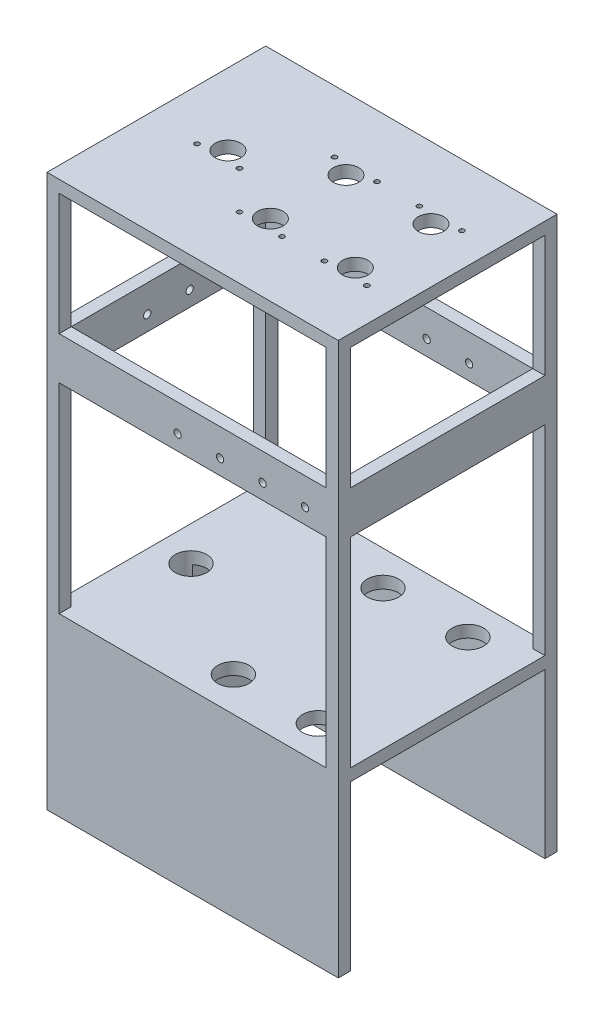
SolidWorks part; units mm, degrees
ref_plane "Front Plane" through (0, 0, 0) normal (0, 0, 1) x (1, 0, 0)
ref_plane "Top Plane" through (0, 0, 0) normal (0, 1, 0) x (1, 0, 0)
ref_plane "Right Plane" through (0, 0, 0) normal (1, 0, 0) x (0, 0, -1)
sketch "Sketch1" plane through (0, 0, 0) normal (0, 1, 0) x (1, 0, 0)
  line L0 (0, 90.15) -> (0, -90.15) construction
  line L1 (-120.075, 0) -> (120.075, 0) construction
  line L2 (-120.075, 90.15) -> (120.075, 90.15)
  line L3 (120.075, 90.15) -> (120.075, -90.15)
  line L4 (120.075, -90.15) -> (-120.075, -90.15)
  line L5 (-120.075, -90.15) -> (-120.075, 90.15)
  dimension "D1" = 240.15
  dimension "D2" = 180.3
extrude "Boss-Extrude1" add sketch "Sketch1" along normal blind 145
sketch "Sketch2" plane through (0, 145, 0) normal (0, 1, 0) x (1, 0, 0)
  line L0 (0, 90.15) -> (0, -90.15) construction
  line L1 (120.075, 90.15) -> (-120.075, 90.15) construction
  line L2 (-120.075, -90.15) -> (120.075, -90.15) construction
  line L3 (-120.075, 0) -> (120.075, 0) construction
  line L4 (-120.075, 90.15) -> (-120.075, -90.15) construction
  line L5 (120.075, -90.15) -> (120.075, 90.15) construction
  line L6 (75.105, -61.65) -> (75.105, -90.15) construction
  line L7 (75.105, -61.65) -> (120.075, -61.65) construction
  line L8 (75.105, -61.65) -> (5.105, -61.65) construction
  circle A0 centre (75.105, -61.65) radius 12.955
  circle A1 centre (5.105, -61.65) radius 12.955
  circle A2 centre (75.105, 61.65) radius 12.955
  circle A3 centre (5.105, 61.65) radius 12.955
  circle A4 centre (-91.515, 0) radius 12.955
  dimension "D3" = 25.91
  dimension "D5" = 25.91
  dimension "D6" = 25.91
  dimension "D7" = 28.56
  dimension "D1" = 44.97
  dimension "D2" = 28.5
  dimension "D4" = 70
extrude "Cut-Extrude1" cut sketch "Sketch2" against normal blind 120
sketch "Sketch3" plane through (120.075, 0, 0) normal (1, 0, 0) x (0, 0, -1)
  line L0 (0, 145) -> (0, 0) construction
  line L1 (-90.15, 145) -> (90.15, 145) construction
  line L2 (-90.15, 72.5) -> (90.15, 72.5) construction
  line L3 (-90.15, 145) -> (-90.15, 0) construction
  line L4 (90.15, 145) -> (90.15, 0) construction
  line L5 (-80.21, 135.06) -> (80.21, 135.06)
  line L6 (80.21, 135.06) -> (80.21, 0)
  line L7 (-90.15, 0) -> (90.15, 0) construction
  line L8 (80.21, 0) -> (-80.21, 0)
  line L9 (-80.21, 0) -> (-80.21, 135.06)
  dimension "D1" = 9.94
  dimension "D2" = 9.94
  dimension "D3" = 9.94
extrude "Cut-Extrude3" cut sketch "Sketch3" against normal blind 220
sketch "Sketch9" plane through (0, 145, 0) normal (0, 1, 0) x (1, 0, 0)
  line L0 (-120.075, 90.15) -> (120.075, 90.15)
  line L1 (120.075, 90.15) -> (120.075, -90.15)
  line L2 (120.075, -90.15) -> (-120.075, -90.15)
  line L3 (-120.075, -90.15) -> (-120.075, 90.15)
extrude "Boss-Extrude3" add sketch "Sketch9" along normal blind 310.134
sketch "Sketch14" plane through (0, 455.134, 0) normal (0, 1, 0) x (1, 0, 0)
  line L0 (75.105, 61.65) -> (75.105, 31.17) construction
  line L1 (-91.515, 0) -> (-61.035, 0) construction
  line L2 (75.105, -61.65) -> (75.105, -31.17) construction
  line L3 (5.105, -61.65) -> (5.105, -31.17) construction
  line L4 (5.105, 61.65) -> (5.105, 31.17) construction
  line L5 (-61.035, 0) -> (193.3968, 0) construction
  line L6 (75.105, 31.17) -> (75.105, -31.17) construction
  line L7 (5.105, 31.17) -> (5.105, -31.17) construction
  line L8 (-61.035, 0) -> (-61.035, -46.2698) construction
  circle A0 centre (5.105, -31.17) radius 10.5
  circle A1 centre (75.105, 31.17) radius 10.5
  circle A3 centre (-61.035, 0) radius 10.5
  circle A5 centre (75.105, -31.17) radius 10.5
  circle A6 centre (92.605, -39.14) radius 2
  circle A7 centre (75.105, -61.65) radius 12.955 construction
  circle A8 centre (57.605, -39.14) radius 2
  circle A9 centre (-91.515, 0) radius 12.955 construction
  circle A10 centre (5.105, -61.65) radius 12.955 construction
  circle A11 centre (5.105, 31.17) radius 10.5
  circle A12 centre (5.105, 61.65) radius 12.955 construction
  circle A13 centre (92.605, 39.14) radius 2
  circle A14 centre (57.605, 39.14) radius 2
  circle A15 centre (22.605, -39.14) radius 2
  circle A16 centre (-12.395, -39.14) radius 2
  circle A17 centre (22.605, 39.14) radius 2
  circle A18 centre (-12.395, 39.14) radius 2
  circle A19 centre (-43.535, -7.97) radius 2
  circle A20 centre (-78.535, -7.97) radius 2
  dimension "D2" = 21
  dimension "D3" = 21
  dimension "D5" = 21
  dimension "D6" = 21
  dimension "D7" = 21
  dimension "D8" = 30.48
  dimension "D9" = 30.48
  dimension "D10" = 30.48
  dimension "D4" = 30.48
  dimension "D12" = 17.5
  dimension "D13" = 4
  dimension "D14" = 17.5
  dimension "D15" = 17.5
  dimension "D16" = 7.97
  dimension "D1" = 30.48
  dimension "D11" = 7.97
extrude "Cut-Extrude6" cut sketch "Sketch14" against normal blind 11
sketch "Sketch15" plane through (0, 0, -90.15) normal (0, 0, -1) x (-1, 0, 0)
  line L0 (-120.075, 455.134) -> (120.075, 455.134) construction
  line L1 (-110.075, 445.134) -> (110.075, 445.134)
  line L2 (-110.075, 445.134) -> (-110.075, 344.894)
  line L3 (-110.075, 344.894) -> (110.075, 344.894)
  line L4 (110.075, 445.134) -> (110.075, 344.894)
  line L5 (-120.075, 455.134) -> (-120.075, 0) construction
  line L6 (120.075, 455.134) -> (120.075, 0) construction
  line L7 (-120.075, 0) -> (120.075, 0) construction
  line L8 (-110.075, 309.844) -> (110.075, 309.844)
  line L9 (-110.075, 309.844) -> (-110.075, 145)
  line L10 (-110.075, 145) -> (110.075, 145)
  line L11 (110.075, 309.844) -> (110.075, 145)
  dimension "D1" = 110.24
  dimension "D2" = 10
  dimension "D3" = 10
  dimension "D4" = 10
  dimension "D5" = 35.05
  dimension "D6" = 10
  dimension "D7" = 10
  dimension "D8" = 145
extrude "Cut-Extrude7" cut sketch "Sketch15" against normal through all
sketch "Sketch16" plane through (120.075, 0, 0) normal (1, 0, 0) x (0, 0, -1)
  line L0 (-90.15, 455.134) -> (-90.15, 0) construction
  line L1 (-80.15, 445.134) -> (80.15, 445.134)
  line L2 (-80.15, 445.134) -> (-80.15, 344.894)
  line L3 (-80.15, 344.894) -> (80.15, 344.894)
  line L4 (80.15, 445.134) -> (80.15, 344.894)
  line L6 (90.15, 455.134) -> (90.15, 0) construction
  line L7 (-90.15, 455.134) -> (90.15, 455.134) construction
  line L9 (-80.15, 145) -> (80.15, 145)
  line L10 (-80.15, 145) -> (-80.15, 309.842)
  line L11 (-80.15, 309.842) -> (80.15, 309.842)
  line L12 (80.15, 145) -> (80.15, 309.842)
  line L13 (-80.21, 0) -> (80.21, 0) construction
  dimension "D1" = 10
  dimension "D2" = 10
  dimension "D3" = 10
  dimension "D4" = 110.24
  dimension "D5" = 10
  dimension "D6" = 10
  dimension "D7" = 145
  dimension "D8" = 35.052
extrude "Cut-Extrude8" cut sketch "Sketch16" against normal through all
sketch "Sketch17" plane through (0, 344.894, 0) normal (0, 1, 0) x (1, 0, 0)
  line L0 (-120.075, 90.15) -> (-120.075, -90.15) construction
  line L1 (-110.075, 80.15) -> (110.075, 80.15)
  line L2 (-110.075, 80.15) -> (-110.075, -80.15)
  line L3 (-110.075, -80.15) -> (110.075, -80.15)
  line L4 (110.075, 80.15) -> (110.075, -80.15)
  line L5 (120.075, 90.15) -> (-120.075, 90.15) construction
  line L6 (120.075, -90.15) -> (120.075, 90.15) construction
  line L7 (-120.075, -90.15) -> (120.075, -90.15) construction
  dimension "D1" = 10
  dimension "D2" = 10
  dimension "D3" = 10
  dimension "D4" = 10
extrude "Cut-Extrude9" cut sketch "Sketch17" against normal up to next
sketch "Sketch18" plane through (0, 0, 90.15) normal (0, 0, 1) x (1, 0, 0)
  line L1 (-110.075, 309.844) -> (110.075, 309.844) construction
  line L2 (120.075, 455.134) -> (120.075, 0) construction
  circle A0 centre (-12.395, 322.394) radius 3
  circle A1 centre (22.605, 322.394) radius 3
  circle A2 centre (57.605, 322.394) radius 3
  circle A3 centre (92.605, 322.394) radius 3
  dimension "D3" = 6
  dimension "D4" = 35
  dimension "D5" = 35
  dimension "D6" = 35
  dimension "D1" = 27.47
  dimension "D2" = 12.55
extrude "Cut-Extrude10" cut sketch "Sketch18" against normal blind 249
sketch "Sketch19" plane through (-120.075, 0, 0) normal (-1, 0, 0) x (0, 0, 1)
  line L0 (-80.15, 309.842) -> (80.15, 309.842) construction
  line L1 (-90.15, 455.134) -> (-90.15, 0) construction
  circle A0 centre (-17.5, 322.392) radius 3
  circle A1 centre (17.5, 322.392) radius 3
  dimension "D1" = 12.55
  dimension "D2" = 72.65
  dimension "D3" = 35
extrude "Cut-Extrude11" cut sketch "Sketch19" against normal blind 104
